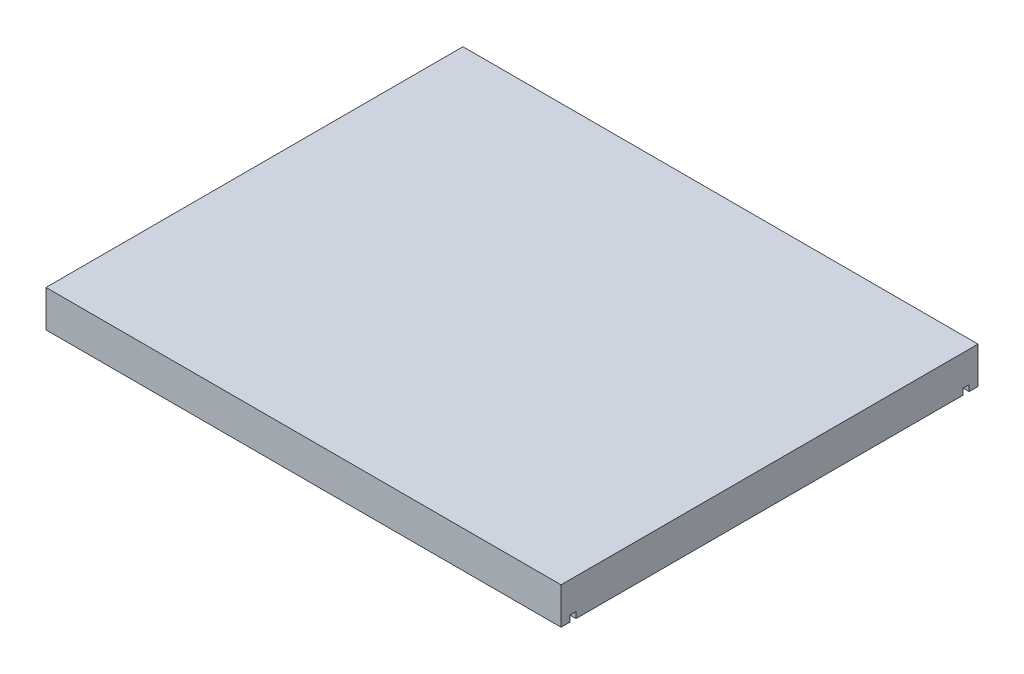
SolidWorks part; units mm, degrees
ref_plane "Front Plane" through (0, 0, 0) normal (0, 0, 1) x (1, 0, 0)
ref_plane "Top Plane" through (0, 0, 0) normal (0, 1, 0) x (1, 0, 0)
ref_plane "Right Plane" through (0, 0, 0) normal (1, 0, 0) x (0, 0, -1)
sketch "Sketch1" plane through (0, 0, 0) normal (0, 1, 0) x (1, 0, 0)
  line L1 (-133.35, -107.95) -> (133.35, -107.95)
  line L2 (-133.35, -107.95) -> (-133.35, 107.95)
  line L3 (-133.35, 107.95) -> (133.35, 107.95)
  line L4 (133.35, -107.95) -> (133.35, 107.95)
  line L5 (-133.35, -107.95) -> (133.35, 107.95) construction
  line L6 (-133.35, 107.95) -> (133.35, -107.95) construction
  point P0 (0, 0)
  dimension "D1" = 266.7
  dimension "D2" = 215.9
extrude "Boss-Extrude1" add sketch "Sketch1" along normal blind 19.05
sketch "Sketch3" plane through (0, 0, 0) normal (1, 0, 0) x (0, 0, -1)
  line L0 (107.95, 0) -> (-107.95, 0) construction
  line L1 (-103.378, 0) -> (-100.203, 0)
  line L2 (-103.378, 0) -> (-103.378, 3.175)
  line L3 (-103.378, 3.175) -> (-100.203, 3.175)
  line L4 (-100.203, 0) -> (-100.203, 3.175)
  line L5 (-107.95, 19.05) -> (-107.95, 0) construction
  dimension "D1" = 3.175
  dimension "D2" = 3.175
  dimension "D3" = 4.572
extrude "Cut-Extrude2" cut sketch "Sketch3" against normal through all both and the other way through all
mirror "Mirror2" about plane through (0, 0, 0) normal (0, 0, 1) of "Cut-Extrude2"
